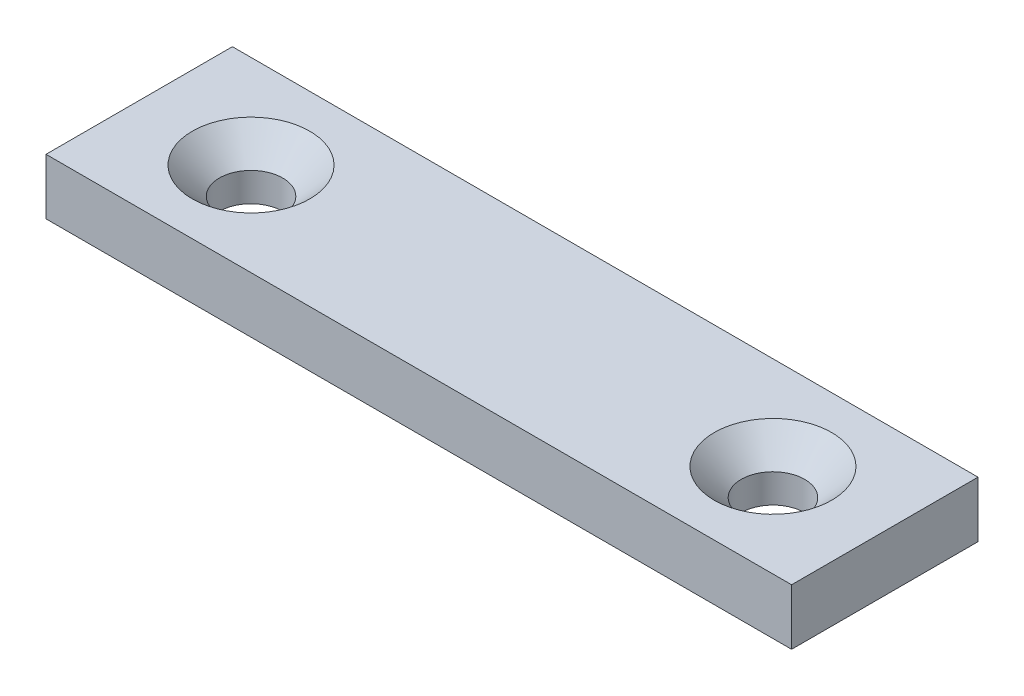
SolidWorks part; units mm, degrees
material "Alloy Steel"
ref_plane "Front Plane" through (0, 0, 0) normal (0, 0, 1) x (1, 0, 0)
ref_plane "Top Plane" through (0, 0, 0) normal (0, 1, 0) x (1, 0, 0)
ref_plane "Right Plane" through (0, 0, 0) normal (1, 0, 0) x (0, 0, -1)
sketch "Sketch1" plane through (0, 0, 0) normal (0, 1, 0) x (1, 0, 0)
  line L1 (-20, -5) -> (20, -5)
  line L2 (-20, -5) -> (-20, 5)
  line L3 (-20, 5) -> (20, 5)
  line L4 (20, -5) -> (20, 5)
  line L5 (-20, -5) -> (20, 5) construction
  line L6 (-20, 5) -> (20, -5) construction
  point P0 (0, 0)
  dimension "D1" = 40
  dimension "D2" = 10
extrude "Boss-Extrude1" add sketch "Sketch1" along normal blind 3
sketch "Sketch2" plane through (0, 3, 0) normal (0, 1, 0) x (1, 0, 0)
  line L0 (-14, 0) -> (14, 0) construction
  point P4 (0, 0)
  point P6 (-14, 0)
  point P7 (14, 0)
  dimension "D1" = 28
hole_wizard "CSK for M3 Countersunk Flat Head Screw1" positions "3DSketch1" profile "Sketch3" countersink size "M3" standard "DIN" end condition through all
sketch3d "3DSketch1"
  point P0 (-14, 3, 0)
  point P3 (14, 3, 0)
sketch "Sketch3" plane through (-14, 3, 0) normal (1, 0, 0) x (0, 0, 1)
  line L0 (0, 0) -> (0, 3)
  line L1 (0, 3) -> (1.7, 3)
  line L2 (1.7, 3) -> (1.7, 1.45)
  line L3 (1.7, 1.45) -> (3.15, 0)
  line L5 (3.15, 0) -> (0, 0)
  line L6 (-1.7, 1.45) -> (-3.15, 0) construction
  line L11 (0, -6.35) -> (0, 107.95) construction
  dimension "Thru Hole Dia." = 3.4
  dimension "Thru Hole Depth" = 3
  dimension "Near C'Sink Dia." = 6.3
  dimension "Near C'Sink Angle" = 90
